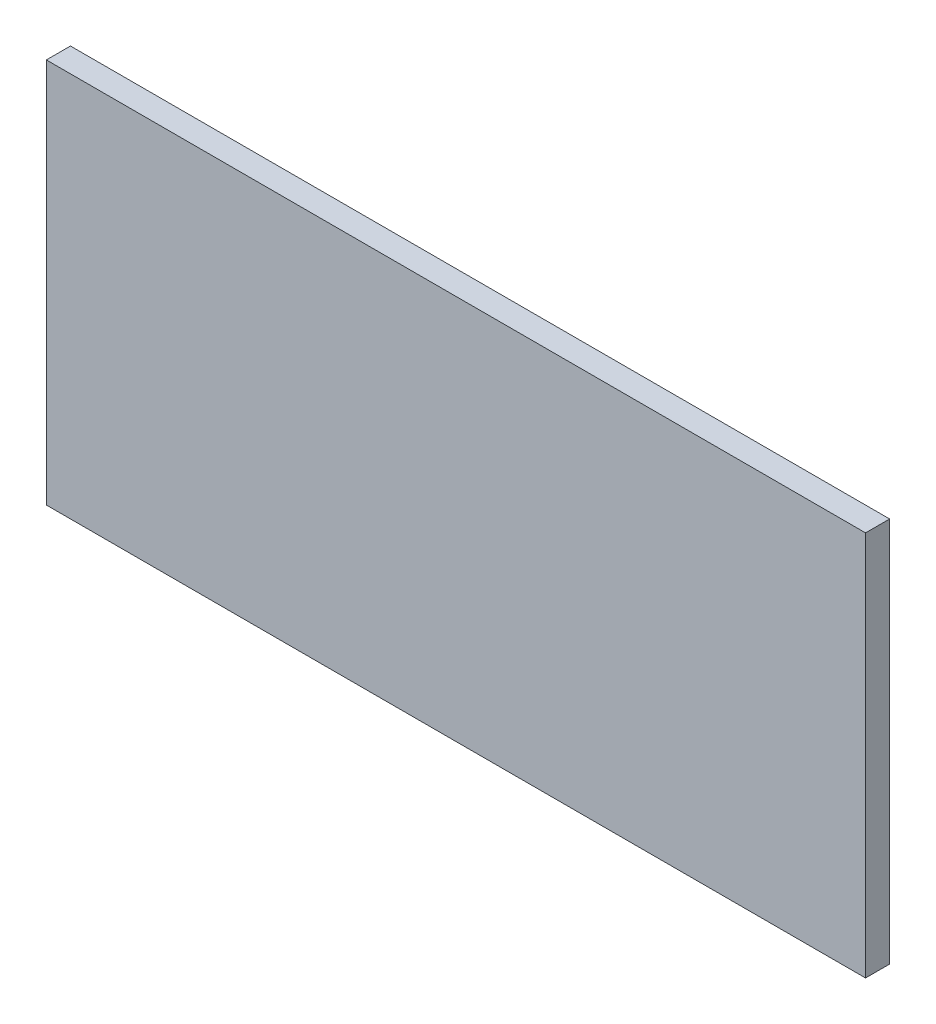
SolidWorks part; units mm, degrees
ref_plane "Front Plane" through (0, 0, 0) normal (0, 0, 1) x (1, 0, 0)
ref_plane "Top Plane" through (0, 0, 0) normal (0, 1, 0) x (1, 0, 0)
ref_plane "Right Plane" through (0, 0, 0) normal (1, 0, 0) x (0, 0, -1)
sketch "Sketch1" plane through (0, 0, 0) normal (0, 0, 1) x (1, 0, 0)
  line L5 (-53.975, -25.4) -> (53.975, -25.4)
  line L6 (-53.975, -25.4) -> (-53.975, 25.4)
  line L7 (-53.975, 25.4) -> (53.975, 25.4)
  line L8 (53.975, -25.4) -> (53.975, 25.4)
  line L9 (-53.975, -25.4) -> (53.975, 25.4) construction
  line L10 (-53.975, 25.4) -> (53.975, -25.4) construction
  point P0 (0, 0)
  dimension "D1" = 107.95
  dimension "D2" = 50.8
extrude "Boss-Extrude1" add sketch "Sketch1" along normal blind 3.175
